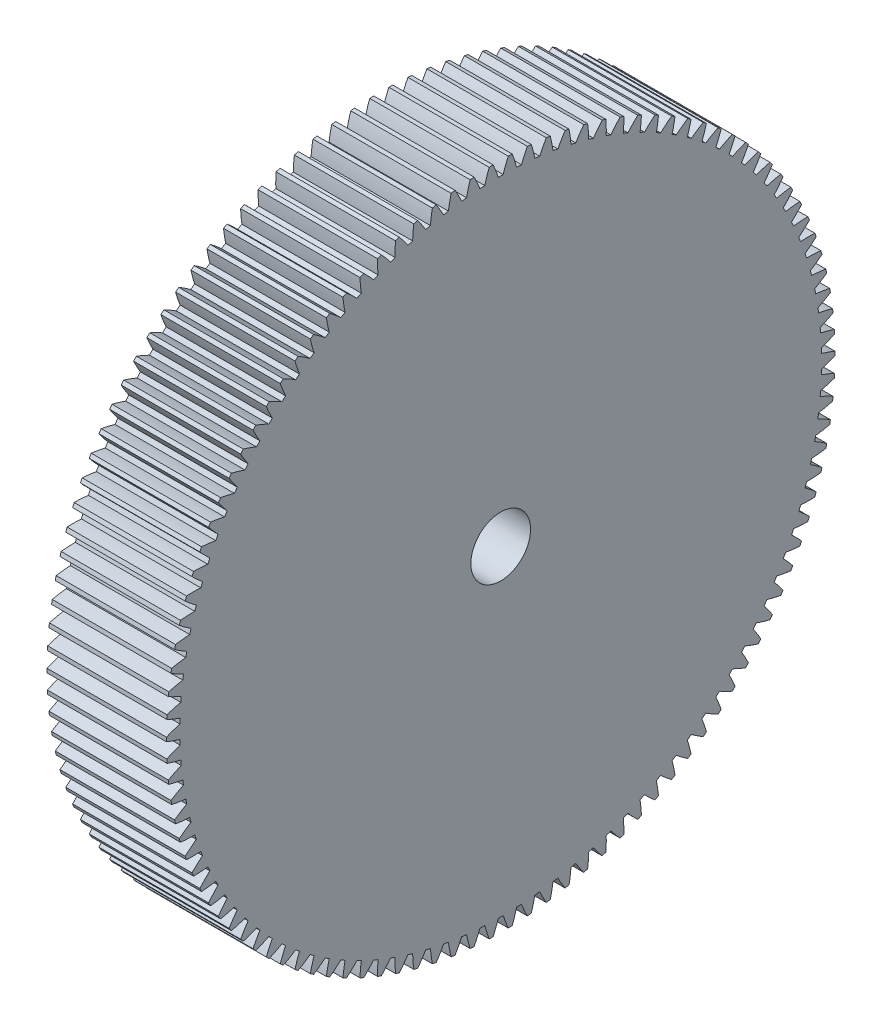
SolidWorks part; units mm, degrees
ref_plane "Plane1" through (0, 0, 0) normal (0, 0, 1) x (1, 0, 0)
ref_plane "Plane2" through (0, 0, 0) normal (0, 1, 0) x (1, 0, 0)
ref_plane "Plane3" through (0, 0, 0) normal (1, 0, 0) x (0, 0, -1)
other "Configuration Table"
sketch "HoldingSke" plane through (0, 0, 0) normal (0, 1, 0) x (1, 0, 0)
  line L0 (0, 0) -> (-0.684, -1.8794)
  line L1 (-15, 0) -> (100, 0) construction
  line L2 (0, 0) -> (-2.1039, 2.3779)
  line L3 (0, 0) -> (-11.863, 4.5341)
  line L4 (0, 0) -> (-2.9537, 8.1152)
  line L5 (0, 0) -> (-46.8476, -17.4728)
  line L6 (0, 0) -> (-8.2896, -5.593)
  line L7 (-2.1039, 2.3779) -> (8.6586, 51.2059)
  line L8 (-76.2, 54.61) -> (-75.3, 54.61)
  line L9 (-71.009, 38.7566) -> (-53.1078, 45.2721)
  line L10 (-76.2, 71.12) -> (104.1128, 71.12)
  line L11 (0, 0) -> (-10, 0)
  line L12 (-76.2, 101.6) -> (-76.181, 101.6)
  line L13 (24.9733, 27.94) -> (52.9518, 28.4284)
  line L14 (24.9733, 27.94) -> (24.9743, 27.94)
  line L15 (24.9733, 27.94) -> (100.4006, 29.5858)
  line L16 (-63.627, -0.5) -> (-12.827, -0.5)
  circle A0 centre (0, 0) radius 2.5
  circle A1 centre (0, 0) radius 26.874
  circle A2 centre (0, 0) radius 37.5
  circle A3 centre (0, 0) radius 2.5
  dimension "MHD" = 53.748
  dimension "Hub_dia" = 75
  dimension "Bore" = 5
  dimension "MBD" = 5
  dimension "Num_teeth" = 110
  dimension "Pitch" = 2
  dimension "Overall_len" = 50
  dimension "Show_teeth" = 110
  dimension "Thickness" = 10
  dimension "OAL" = 50.0001
  dimension "T_dim" = 0.9
  dimension "Ap" = 20
  dimension "H" = 19.05
  dimension "Pitch_radius" = 180.3128
  dimension "Width" = 10
  dimension "Backlash" = 0.019
  dimension "Addendum_fac" = 1
  dimension "Dedendum_fac" = 1.25
  dimension "Clearance_fac" = 0.25
  dimension "Dedendum_add" = 0.001
  dimension "Module" = 0.5
sketch "BasProSke" plane through (0, 0, 0) normal (0, 1, 0) x (1, 0, 0)
  line L0 (-10, 0) -> (60, 0) construction
  line L1 (0, 0) -> (0, 28)
  line L2 (0, 0) -> (10, 0)
  line L3 (10, 0) -> (10, 28)
  line L4 (10, 28) -> (0, 28)
  dimension "Thickness" = 10
  dimension "Diameter" = 56
revolve "Base-Revolve" add sketch "BasProSke" angle 360 about L0
sketch "TooCutSke" plane through (0, 0, 0) normal (1, 0, 0) x (0, 0, -1)
  line L1 (0, 0) -> (0, 107) construction
  line L2 (0, 0) -> (-0.4259, 27.4967) construction
  line L3 (0, 0) -> (-1.5704, 54.9729) construction
  line L4 (-0.4259, 27.4967) -> (-0.7852, 27.4864) construction
  arc A0 (0.2061, 26.8732) -> (-0.2061, 26.8732) centre (0, 0) ccw
  arc A1 (0.6431, 28.018) -> (-0.6431, 28.018) centre (0, 0) ccw
  circle A2 centre (0, 0) radius 27.5 construction
  circle A3 centre (0, 0) radius 25.8415 construction
  arc A4 (-0.2061, 26.8732) -> (-0.6431, 28.018) centre (-10.6854, 23.5289) ccw
  arc A5 (0.6431, 28.018) -> (0.2061, 26.8732) centre (10.6854, 23.5289) ccw
  dimension "Root_dia" = 53.748
  dimension "Overcut_dia" = 56.0508
  dimension "Pitch_dia" = 55
  dimension "Base_dia" = 51.6831
  dimension "Flank_rad" = 11
  dimension "Half_ang" = 1.636
  dimension "Half_CT" = 0.3594
extrude "ToothCut" cut sketch "TooCutSke" along normal through all
fillet "Breaks" [suppressed] radius 0.01
fillet "RootFillets" [suppressed] radius 0.126
pattern_circular "TeethCuts" count 110 every 3.273 about axis through (-10, 0, 0) along (1, 0, 0) of "ToothCut", "RootFillets", "Breaks"
sketch "HubNeaOneSke" plane through (0, 0, 0) normal (-1, 0, 0) x (0, 0, 1)
  circle A0 centre (0, 0) radius 26.874
  dimension "Diameter" = 53.748
extrude "HubNearOne" [suppressed] add sketch "HubNeaOneSke" along normal blind 40.0001
sketch "HubNeaBotSke" plane through (0, 0, 0) normal (-1, 0, 0) x (0, 0, 1)
  circle A0 centre (0, 0) radius 26.874
  dimension "Diameter" = 53.748
extrude "HubNearBoth" [suppressed] add sketch "HubNeaBotSke" along normal blind 20
ref_plane "FarPln" through (10, 0, 0) normal (1, 0, 0) x (0, 0, -1)
sketch "HubFarSke" plane through (10, 0, 0) normal (1, 0, 0) x (0, 0, -1)
  circle A0 centre (0, 0) radius 26.874
  dimension "Diameter" = 53.748
extrude "HubFar" [suppressed] add sketch "HubFarSke" along normal blind 20
sketch "BorSke" plane through (0, 0, 0) normal (1, 0, 0) x (0, 0, -1)
  circle A0 centre (0, 0) radius 2.5
  dimension "Diameter" = 5
extrude "Bore" cut sketch "BorSke" along normal mid plane 100.0001
sketch "KeySke" plane through (0, 0, 0) normal (1, 0, 0) x (0, 0, -1)
  line L0 (-1, 0) -> (-1, 3.4)
  line L1 (-1, 3.4) -> (1, 3.4)
  line L2 (1, 3.4) -> (1, 0)
  line L3 (0, 0) -> (0, 34) construction
  line L4 (-1, 0) -> (1, 0)
  dimension "Offset" = 3.4
  dimension "Width" = 2
extrude "Keyway" [suppressed] cut sketch "KeySke" along normal mid plane 100.0001
pattern_circular "Keyway2" [suppressed] count 2 every 90 about axis through (-10, 0, 0) along (1, 0, 0)
equation "' \"Module@HoldingSke\" = 6.35"
equation "' \"Num_teeth@HoldingSke\" = 12"
equation "' \"Ap@HoldingSke\" =  20"
equation "' \"Ap@HoldingSke\" = 20"
equation "' \"Width@HoldingSke\" = 0.5 * 25.4"
equation "' \"Hub_dia@HoldingSke\"= 1 * 25.4"
equation "' \"Hub_dia@HoldingSke\" = 1 * 25.4"
equation "' \"Overall_len@HoldingSke\" = 1.0 * 25.4"
equation "' \"Bore@HoldingSke\" = 0.75 * 25.4"
equation "' \"T_dim@HoldingSke\" = 0.1 * 25.4"
equation "' \"Width@KeySke\" = 0.25 * 25.4"
equation "' \"Show_teeth@HoldingSke\" = 13"
equation "' \"Backlash@HoldingSke\" = 0.009 * 25.4"
equation "' \"Addendum_fac@HoldingSke\" = 1.0"
equation "' \"Dedendum_fac@HoldingSke\" = 1.25"
equation "' \"Dedendum_add@HoldingSke\" = 0.00005 * 25.4"
equation "' \"Clearance_fac@HoldingSke\" = 0.25"
equation "\"Pitch@HoldingSke\" = 1 / \"Module@HoldingSke\""
equation "\"Overcut_dia@TooCutSke\" = (\"Num_teeth@HoldingSke\" + 2 * \"Addendum_fac@HoldingSke\") / \"Pitch@HoldingSke\" + 0.002 * 25.4"
equation "\"Pitch_dia@TooCutSke\" = \"Num_teeth@HoldingSke\" / \"Pitch@HoldingSke\""
equation "\"Base_dia@TooCutSke\" = \"Num_teeth@HoldingSke\" / \"Pitch@HoldingSke\" * cos((\"Ap@HoldingSke\"  * 3.14159265 / 180))"
equation "\"Root_dia@TooCutSke\" = (\"Num_teeth@HoldingSke\" + 2) / \"Pitch@HoldingSke\" - 2 * (\"Addendum_fac@HoldingSke\" + \"Dedendum_fac@HoldingSke\") / \"Pitch@HoldingSke\" - \"Dedendum_add@HoldingSke\" * 2"
equation "\"Half_ang@TooCutSke\" = 180 / \"Num_teeth@HoldingSke\""
equation "\"Half_CT@TooCutSke\" = \"Num_teeth@HoldingSke\" / \"Pitch@HoldingSke\" * sin((3.14159265 / 2 / \"Num_teeth@HoldingSke\")) / 2 - 7 * \"Backlash@HoldingSke\" / 4"
equation "\"Flank_rad@TooCutSke\" = \"Num_teeth@HoldingSke\" / \"Pitch@HoldingSke\" / 5"
equation "\"Radius@RootFillets\" = \"Clearance_fac@HoldingSke\" / \"Pitch@HoldingSke\" + \"Dedendum_add@HoldingSke\""
equation "\"Break_rad@Breaks\" = 0.02 / \"Pitch@HoldingSke\""
equation "\"Thickness@HoldingSke\" = \"Width@HoldingSke\""
equation "\"OAL@HoldingSke\" = \"Thickness@HoldingSke\""
equation "\"MHD@HoldingSke\" = (\"Num_teeth@HoldingSke\" + 2) / \"Pitch@HoldingSke\" - 2 * (\"Addendum_fac@HoldingSke\" + \"Dedendum_fac@HoldingSke\")  / \"Pitch@HoldingSke\" - \"Dedendum_add@HoldingSke\" * 2"
equation "\"MBD@HoldingSke\" = (\"Num_teeth@HoldingSke\" + 2) / \"Pitch@HoldingSke\" - 2 * (\"Addendum_fac@HoldingSke\" + \"Dedendum_fac@HoldingSke\")  / \"Pitch@HoldingSke\" - \"Dedendum_add@HoldingSke\" * 2 - 0.002 * 25.4"
equation "\"MHD@HoldingSke\" = ((sgn( \"MHD@HoldingSke\" - \"Hub_dia@HoldingSke\" )-1)*( \"MHD@HoldingSke\" - \"Hub_dia@HoldingSke\" ))/-2+ \"Hub_dia@HoldingSke\""
equation "\"MBD@HoldingSke\" = ((sgn( \"MBD@HoldingSke\" - \"Bore@HoldingSke\" )-1)*( \"MBD@HoldingSke\" - \"Bore@HoldingSke\" ))/-2+ \"Bore@HoldingSke\""
equation "\"OAL@HoldingSke\" = ((sgn( \"OAL@HoldingSke\" - \"Overall_len@HoldingSke\" )+1)*( \"OAL@HoldingSke\" - \"Overall_len@HoldingSke\" ))/2 + \"Overall_len@HoldingSke\" + 0.000002 * 25.4"
equation "\"Num_teeth@TeethCuts\" = int( \"Show_teeth@HoldingSke\" ) + 1"
equation "\"Num_teeth@TeethCuts\" = ((sgn( \"Num_teeth@TeethCuts\" - \"Num_teeth@HoldingSke\" )-1)*( \"Num_teeth@TeethCuts\" - \"Num_teeth@HoldingSke\" ))/-2+ \"Num_teeth@HoldingSke\""
equation "\"Num_teeth@TeethCuts\" = ((sgn( \"Num_teeth@TeethCuts\" - 2.0)+1)*( \"Num_teeth@TeethCuts\" - 2.0))/2 +2.0"
equation "\"Angle@TeethCuts\" = 360.0 / \"Num_teeth@HoldingSke\""
equation "\"Diameter@BasProSke\" = (\"Num_teeth@HoldingSke\" + 2 * \"Addendum_fac@HoldingSke\") / \"Pitch@HoldingSke\""
equation "\"Thickness@BasProSke\"  = \"Thickness@HoldingSke\""
equation "' \"Fillet_rad@BasProSke\" =  \"Thickness@HoldingSke\" * 0.05"
equation "' \"Fillet_rad@BasProSke\" = \"Thickness@HoldingSke\" * 0.05"
equation "\"MHD@HoldingSke\" = ((sgn( \"MHD@HoldingSke\" - \"Root_dia@TooCutSke\" )-1)*( \"MHD@HoldingSke\" - \"Root_dia@TooCutSke\" ))/-2+ \"Root_dia@TooCutSke\""
equation "\"Diameter@HubNeaOneSke\" = \"MHD@HoldingSke\""
equation "\"Length@HubNearOne\" = \"OAL@HoldingSke\" - \"Thickness@BasProSke\""
equation "\"Diameter@HubNeaBotSke\" = \"MHD@HoldingSke\""
equation "\"Length@HubNearBoth\" = ( \"OAL@HoldingSke\" - \"Thickness@BasProSke\" ) / 2.0"
equation "\"Thickness@FarPln\" = \"Thickness@BasProSke\""
equation "\"Diameter@HubFarSke\" = \"MHD@HoldingSke\""
equation "\"Length@HubFar\" = ( \"OAL@HoldingSke\" - \"Thickness@BasProSke\" ) / 2.0"
equation "\"Diameter@BorSke\" = \"MBD@HoldingSke\""
equation "\"D1@Bore\" = \"OAL@HoldingSke\" * 2.0"
equation "\"D1@Keyway\" = \"OAL@HoldingSke\" * 2.0"
equation "\"Offset@KeySke\" = \"T_dim@HoldingSke\" + \"MBD@HoldingSke\" / 2.0"
